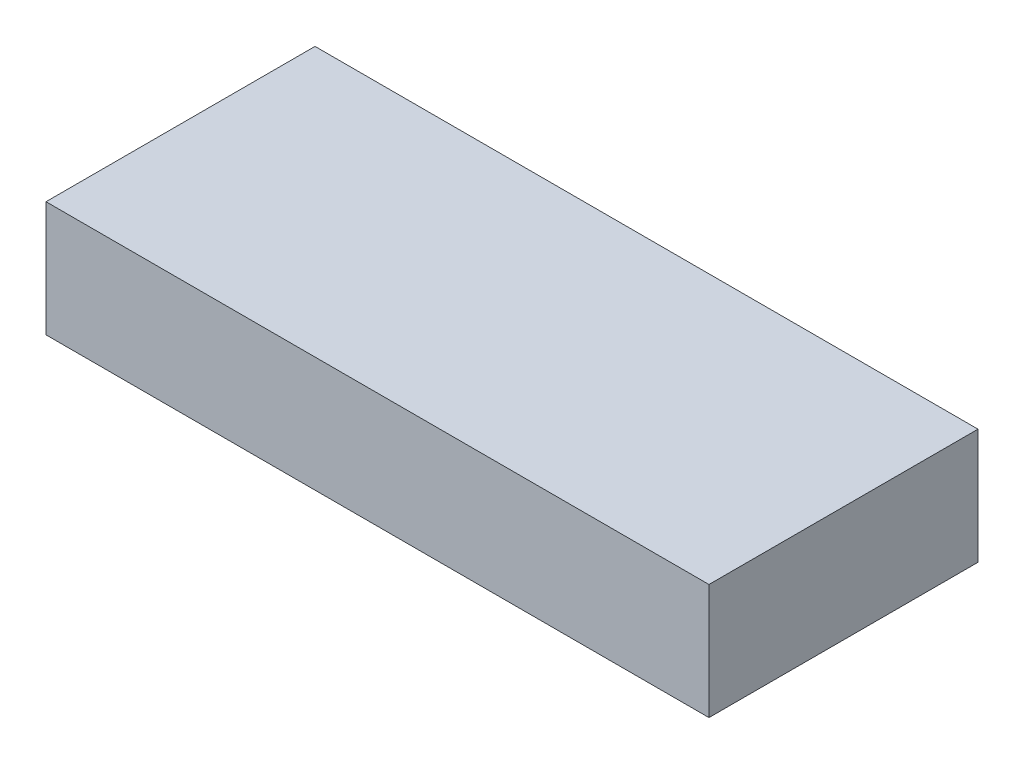
SolidWorks part; units mm, degrees
material "Pine"
ref_plane "Front Plane" through (0, 0, 0) normal (0, 0, 1) x (1, 0, 0)
ref_plane "Top Plane" through (0, 0, 0) normal (0, 1, 0) x (1, 0, 0)
ref_plane "Right Plane" through (0, 0, 0) normal (1, 0, 0) x (0, 0, -1)
sketch "Sketch1" plane through (0, 0, 0) normal (0, 1, 0) x (1, 0, 0)
  line L1 (0, 0) -> (219.075, 0)
  line L2 (0, 0) -> (0, 88.9)
  line L3 (0, 88.9) -> (219.075, 88.9)
  line L4 (219.075, 0) -> (219.075, 88.9)
  dimension "D1" = 88.9
  dimension "D2" = 219.075
extrude "Boss-Extrude1" add sketch "Sketch1" along normal blind 38.1
